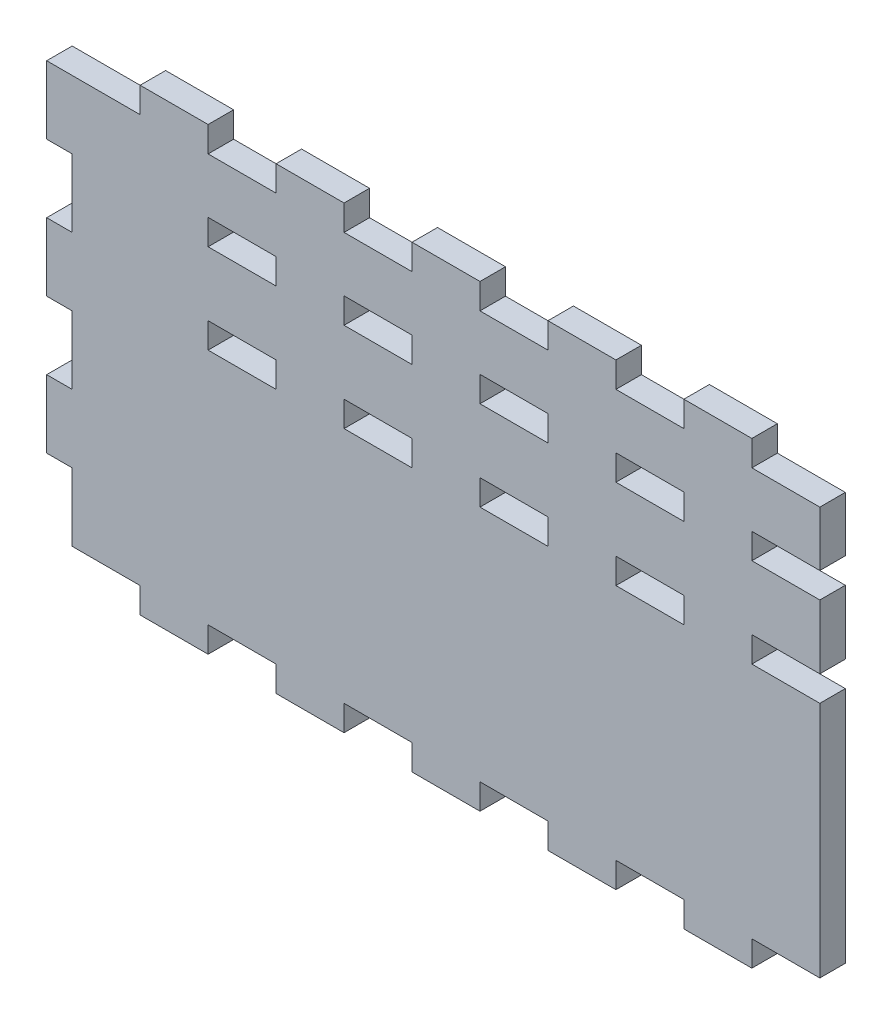
SolidWorks part; units mm, degrees
ref_plane "Front Plane" through (0, 0, 0) normal (0, 0, 1) x (1, 0, 0)
ref_plane "Top Plane" through (0, 0, 0) normal (0, 1, 0) x (1, 0, 0)
ref_plane "Right Plane" through (0, 0, 0) normal (1, 0, 0) x (0, 0, -1)
sketch "Sketch1" plane through (0, 0, 0) normal (0, 0, 1) x (1, 0, 0)
  line L1 (-139.7, -76.2) -> (139.7, -76.2)
  line L2 (-139.7, -76.2) -> (-139.7, 76.2)
  line L3 (-139.7, 76.2) -> (139.7, 76.2)
  line L4 (139.7, -76.2) -> (139.7, 76.2)
  line L5 (-139.7, -76.2) -> (139.7, 76.2) construction
  line L6 (-139.7, 76.2) -> (139.7, -76.2) construction
  point P0 (0, 0)
  dimension "D1" = 279.4
  dimension "D2" = 152.4
extrude "Boss-Extrude1" add sketch "Sketch1" along normal blind 9.525
sketch "Sketch2" plane through (0, -76.2, 0) normal (0, -1, 0) x (1, 0, 0)
  line L0 (-139.7, 0) -> (139.7, 0) construction
  line L1 (-114.3, 0) -> (-88.9, 0)
  line L2 (-114.3, 0) -> (-114.3, 9.525)
  line L3 (-114.3, 9.525) -> (-88.9, 9.525)
  line L4 (-88.9, 0) -> (-88.9, 9.525)
  line L5 (-139.7, 9.525) -> (139.7, 9.525) construction
  line L6 (-139.7, 9.525) -> (-139.7, 0) construction
  point P10 (-139.7, 4.7625)
  dimension "D1" = 25.4
  dimension "D2" = 25.4
extrude "Boss-Extrude2" add sketch "Sketch2" along normal blind 9.525
pattern_linear "LPattern1" count 5 spacing 50.8 along (1, 0, 0) of "Boss-Extrude2"
mirror "Mirror1" about plane through (0, 0, 0) normal (0, 1, 0) of "LPattern1", "Boss-Extrude2"
sketch "Sketch3" plane through (-139.7, 0, 0) normal (-1, 0, 0) x (0, 0, 1)
  line L0 (0, 76.2) -> (0, -76.2) construction
  line L1 (9.525, 76.2) -> (0, 76.2)
  line L2 (9.525, 76.2) -> (9.525, 50.8)
  line L3 (9.525, 50.8) -> (0, 50.8)
  line L4 (0, 76.2) -> (0, 50.8)
  dimension "D1" = 25.4
extrude "Boss-Extrude3" add sketch "Sketch3" along normal blind 9.525
pattern_linear "LPattern2" count 3 spacing 50.8 along (0, -1, 0) of "Boss-Extrude3"
sketch "Sketch4" plane through (0, 0, 0) normal (0, 0, -1) x (-1, 0, 0)
  line L1 (-139.7, 12.7) -> (-114.3, 12.7)
  line L2 (-139.7, 12.7) -> (-139.7, 22.225)
  line L3 (-139.7, 22.225) -> (-114.3, 22.225)
  line L4 (-114.3, 12.7) -> (-114.3, 22.225)
  line L5 (-114.3, -76.2) -> (-139.7, -76.2) construction
  line L6 (-139.7, -76.2) -> (-139.7, 76.2) construction
  dimension "D1" = 25.4
  dimension "D2" = 9.525
  dimension "D4" = 88.9
extrude "Cut-Extrude1" cut sketch "Sketch4" against normal through all
pattern_linear "LPattern3" count 5 spacing 50.8 along (-1, 0, 0) of "Cut-Extrude1"
sketch "Sketch5" plane through (0, 0, 9.525) normal (0, 0, 1) x (1, 0, 0)
  line L0 (-88.9, 12.7) -> (-88.9, 22.225) construction
  line L1 (-63.5, 55.6678) -> (-88.9, 55.6678)
  line L2 (-63.5, 55.6678) -> (-63.5, 46.1428)
  line L3 (-63.5, 46.1428) -> (-88.9, 46.1428)
  line L4 (-88.9, 55.6678) -> (-88.9, 46.1428)
  dimension "D1" = 25.4
  dimension "D2" = 9.525
extrude "Cut-Extrude2" cut sketch "Sketch5" against normal through all
pattern_linear "LPattern4" count 5 spacing 50.8 along (1, 0, 0) of "Cut-Extrude2"
